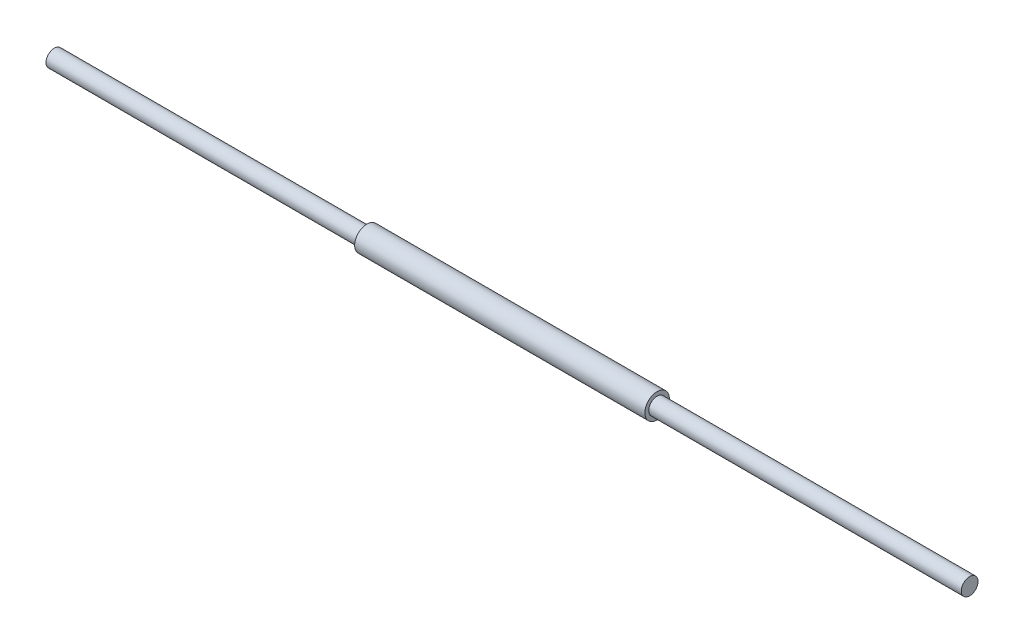
SolidWorks part; units mm, degrees
material "AISI 1020"
ref_plane "Front Plane" through (0, 0, 0) normal (0, 0, 1) x (1, 0, 0)
ref_plane "Top Plane" through (0, 0, 0) normal (0, 1, 0) x (1, 0, 0)
ref_plane "Right Plane" through (0, 0, 0) normal (1, 0, 0) x (0, 0, -1)
sketch "Sketch1" plane through (0, 0, 0) normal (0, 1, 0) x (1, 0, 0)
  line L0 (-260.35, 0) -> (260.35, 0)
  line L2 (-260.35, 0) -> (-260.35, 4.7625)
  line L3 (-260.35, 4.7625) -> (-82.55, 4.7625)
  line L4 (260.35, 0) -> (260.35, 4.7625)
  line L5 (82.55, 4.7625) -> (82.55, 6.985)
  line L9 (-82.55, 6.985) -> (82.55, 6.985)
  line L11 (82.55, 4.7625) -> (260.35, 4.7625)
  line L13 (-82.55, 4.7625) -> (-82.55, 6.985)
  point P0 (0, 0)
  point P6 (0, 0)
  dimension "D2" = 520.7
  dimension "D4" = 165.1
revolve "Revolve1" add sketch "Sketch1" angle 360 about L0
equation "\"A\"= 20.5"
equation "\"B\"= 6.5"
equation "\"C\"= 36deg"
equation "\"D4@Sketch1\"=\"B\""
